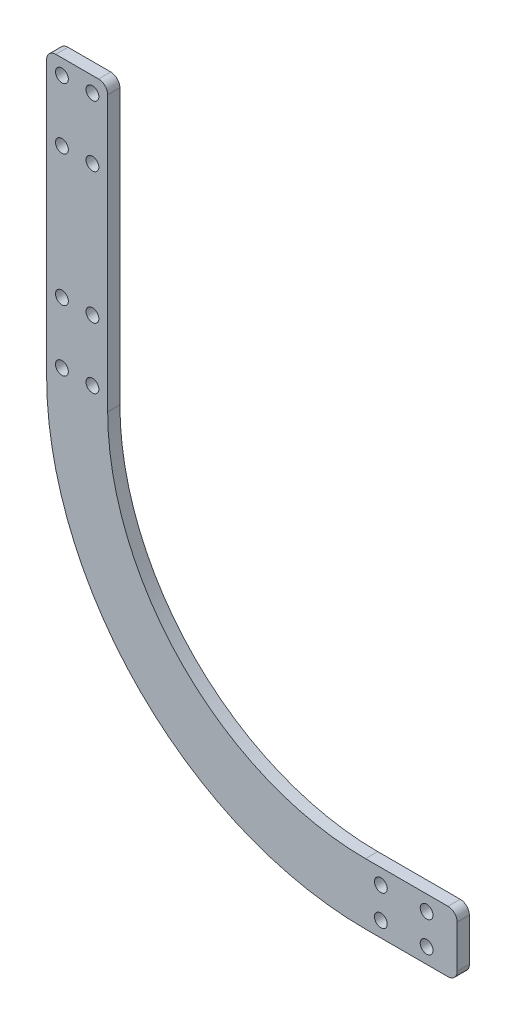
SolidWorks part; units mm, degrees
material "Thornel Mat VMA"
ref_plane "前视基准面" through (0, 0, 0) normal (0, 0, 1) x (1, 0, 0)
ref_plane "上视基准面" through (0, 0, 0) normal (0, 1, 0) x (1, 0, 0)
ref_plane "右视基准面" through (0, 0, 0) normal (1, 0, 0) x (0, 0, -1)
sketch "草图1" plane through (0, 0, 0) normal (0, 0, 1) x (1, 0, 0)
  line L0 (0, 0) -> (0, -20)
  line L1 (-104.5, 84.5) -> (-84.5, 84.5)
  line L2 (-104.5, 84.5) -> (-104.5, 100.6591) construction
  line L3 (-84.5, 84.5) -> (-84.5, 99.1923) construction
  arc A0 (0, -20) -> (-104.5, 84.5) centre (0, 84.5) cw
  arc A1 (-84.5, 84.5) -> (0, 0) centre (0, 84.5) ccw
  dimension "D2" = 84.5
  dimension "D1" = 20
extrude "凸台-拉伸1" add sketch "草图1" along normal blind 4
sketch "草图2" plane through (0, 0, 4) normal (0, 0, 1) x (1, 0, 0)
  line L1 (-66.8216, 17.6784) -> (-35422.1607, -35337.6607) construction
  arc A0 (-84.5, 84.5) -> (0, 0) centre (0, 84.5) ccw construction
  arc A1 (-84.5, 84.5) -> (0, 0) centre (0, 84.5) ccw construction
  arc A2 (-94.5, 84.5) -> (0, -10) centre (0, 84.5) ccw construction
  circle A3 centre (-66.8216, 17.6784) radius 2.1
  circle A4 centre (-90.1502, 56.1593) radius 2.1
  circle A5 centre (-28.3407, -5.6502) radius 2.1
  point P8 (-66.8216, 17.6784)
  dimension "D2" = 4.2
  dimension "D3" = 45
  dimension "D1" = 10
extrude "切除-拉伸1" [suppressed] cut sketch "草图2" against normal through all
sketch "草图3" plane through (0, 0, 4) normal (0, 0, 1) x (1, 0, 0)
  line L0 (-104.5, 84.5) -> (-84.5, 84.5)
  line L1 (-104.5, 84.5) -> (-104.5, 119.5)
  line L4 (-84.5, 102) -> (-104.5, 102) construction
  line L5 (-94.5, 84.5) -> (-94.5, 119.5) construction
  line L6 (-104.5, 119.5) -> (-92, 141.1506)
  line L7 (-92, 141.1506) -> (-70.3494, 128.6506)
  line L8 (-70.3494, 128.6506) -> (-84.5, 104.141)
  line L9 (-84.5, 84.5) -> (-84.5, 104.141)
  point P270 (-94.5, 102)
  dimension "D1" = 35
  dimension "D2" = 150
  dimension "D3" = 25
  dimension "D4" = 25
extrude "凸台-拉伸2" [suppressed] add sketch "草图3" against normal up to surface (4 mm away)
fillet "圆角1" [suppressed] radius 30
sketch "草图4" [suppressed] plane through (0, 0, 4) normal (0, 0, 1) x (1, 0, 0)
  line L0 (-92, 141.1506) -> (-70.3494, 128.6506)
  line L1 (-92, 141.1506) -> (-57, 201.7724)
  line L2 (-70.3494, 128.6506) -> (-35.3494, 189.2724)
  line L3 (-57, 201.7724) -> (-35.3494, 189.2724)
  line L4 (-52.8494, 158.9615) -> (-74.5, 171.4615) construction
  line L5 (-81.1747, 134.9006) -> (-46.1747, 195.5224) construction
  line L6 (0, 0) -> (0, -20)
  line L7 (0, 0) -> (25, 0)
  line L8 (0, -20) -> (25, -20)
  line L9 (25, 0) -> (25, -20)
  line L10 (12.5, -20) -> (12.5, 0) construction
  line L11 (0, -10) -> (25, -10) construction
  line L12 (-63.0048, 176.3718) -> (-53.0048, 193.6923) construction
  line L13 (5, -5) -> (20, -5) construction
  line L14 (5, -5) -> (5, -15) construction
  line L15 (5, -15) -> (20, -15) construction
  line L16 (20, -5) -> (20, -15) construction
  line L17 (12.5, -15) -> (12.5, -5) construction
  line L18 (5, -10) -> (20, -10) construction
  line L19 (-63.0048, 176.3718) -> (-54.3446, 171.3718) construction
  line L20 (-53.0048, 193.6923) -> (-44.3446, 188.6923) construction
  line L21 (-54.3446, 171.3718) -> (-44.3446, 188.6923) construction
  line L22 (-63.0048, 176.3718) -> (-44.3446, 188.6923) construction
  line L23 (-53.0048, 193.6923) -> (-54.3446, 171.3718) construction
  line L24 (-58.0048, 185.032) -> (-49.3446, 180.032) construction
  circle A0 centre (5, -5) radius 2.1
  circle A1 centre (20, -5) radius 2.1
  circle A2 centre (20, -15) radius 2.1
  circle A3 centre (5, -15) radius 2.1
  circle A4 centre (-63.0048, 176.3718) radius 2.1
  circle A5 centre (-54.3446, 171.3718) radius 2.1
  circle A6 centre (-44.3446, 188.6923) radius 2.1
  circle A7 centre (-53.0048, 193.6923) radius 2.1
  point P0 (12.5, -10)
  point P17 (-53.6747, 182.532)
  point P170 (12.5, -10)
  point P214 (-63.6747, 165.2115)
  dimension "D5" = 4.2
  dimension "D8" = 4.2
  dimension "D1" = 70
  dimension "D2" = 25
  dimension "D3" = 10
  dimension "D4" = 15
  dimension "D6" = 10
  dimension "D7" = 20
  dimension "D9" = 5
extrude "凸台-拉伸3" [suppressed] add sketch "草图4" against normal up to surface (4 mm away)
sketch "草图5" plane through (0, 0, 4) normal (0, 0, 1) x (1, 0, 0)
  line L0 (-104.5, 84.5) -> (-84.5, 84.5)
  line L1 (-104.5, 84.5) -> (-104.5, 177.5)
  line L2 (-84.5, 84.5) -> (-84.5, 177.5)
  line L3 (-104.5, 177.5) -> (-84.5, 177.5)
  line L4 (-84.5, 131) -> (-104.5, 131) construction
  line L5 (-94.5, 84.5) -> (-94.5, 177.5) construction
  arc A0 (-84.5, 84.5) -> (0, 0) centre (0, 84.5) ccw construction
  point P210 (-94.5, 131)
  dimension "D1" = 93
extrude "凸台-拉伸4" add sketch "草图5" against normal up to surface (4 mm away) up to face at (-57.0358, 27.4642, 0)
sketch "草图6" plane through (0, 0, 4) normal (0, 0, 1) x (1, 0, 0)
  line L0 (0, 0) -> (0, -20)
  line L1 (0, 0) -> (30, 0)
  line L2 (0, -20) -> (30, -20)
  line L3 (30, 0) -> (30, -20)
  line L4 (15, -20) -> (15, 0) construction
  line L5 (0, -10) -> (30, -10) construction
  point P186 (15, -10)
  dimension "D1" = 30
extrude "凸台-拉伸5" add sketch "草图6" against normal up to surface (4 mm away) up to face at (-69.5239, 77.4761, 0)
sketch "草图7" plane through (0, 0, 4) normal (0, 0, 1) x (1, 0, 0)
  line L0 (-84.5, 177.5) -> (-104.5, 177.5) construction
  line L1 (-104.5, 177.5) -> (-104.5, 84.5) construction
  line L2 (-186.3207, 204.9537) -> (-182.9182, 201.5512) construction
  line L3 (-94.5, 177.5) -> (-94.5, 78.1608) construction
  line L4 (30, -10) -> (-7.3567, -10) construction
  line L5 (30, -20) -> (30, 0) construction
  line L7 (-99.5, 172.5) -> (-89.5, 172.5) construction
  line L8 (-99.5, 172.5) -> (-99.5, 152.5) construction
  line L9 (-99.5, 152.5) -> (-89.5, 152.5) construction
  line L10 (-89.5, 172.5) -> (-89.5, 152.5) construction
  line L11 (-94.5, 152.5) -> (-94.5, 172.5) construction
  line L12 (-99.5, 162.5) -> (-89.5, 162.5) construction
  line L13 (-99.5, 109.5) -> (-89.5, 109.5) construction
  line L14 (-99.5, 109.5) -> (-99.5, 89.5) construction
  line L15 (-99.5, 89.5) -> (-89.5, 89.5) construction
  line L16 (-89.5, 109.5) -> (-89.5, 89.5) construction
  line L17 (-94.5, 89.5) -> (-94.5, 109.5) construction
  line L18 (-99.5, 99.5) -> (-89.5, 99.5) construction
  circle A0 centre (-99.5, 109.5) radius 2.1
  circle A1 centre (-89.5, 109.5) radius 2.1
  circle A2 centre (-89.5, 89.5) radius 2.1
  circle A3 centre (-99.5, 89.5) radius 2.1
  circle A4 centre (-99.5, 152.5) radius 2.1
  circle A5 centre (-89.5, 152.5) radius 2.1
  circle A6 centre (-89.5, 172.5) radius 2.1
  circle A7 centre (-99.5, 172.5) radius 2.1
  circle A9 centre (20, -15) radius 2.1
  circle A11 centre (20, -5) radius 2.1
  circle A13 centre (5, -5) radius 2.1
  circle A15 centre (5, -15) radius 2.1
  point P24 (-94.5, 99.5)
  point P109 (-94.5, 162.5)
  dimension "D1" = 4.2
  dimension "D2" = 20
  dimension "D3" = 20
  dimension "D4" = 5
  dimension "D5" = 5
  dimension "D6" = 10
  dimension "D7" = 15
  dimension "D8" = 10
  dimension "D9" = 10
  dimension "D10" = 63
  dimension "D11" = 10
extrude "切除-拉伸2" cut sketch "草图7" against normal through all
sketch "草图8" plane through (0, 0, 4) normal (0, 0, 1) x (1, 0, 0)
  line L0 (20, -5) -> (20, -15) construction
fillet "圆角2" radius 3 4 edges at (-84.5, 177.5, 2) (-104.5, 177.5, 2) (30, 0, 2) (30, -20, 2)
